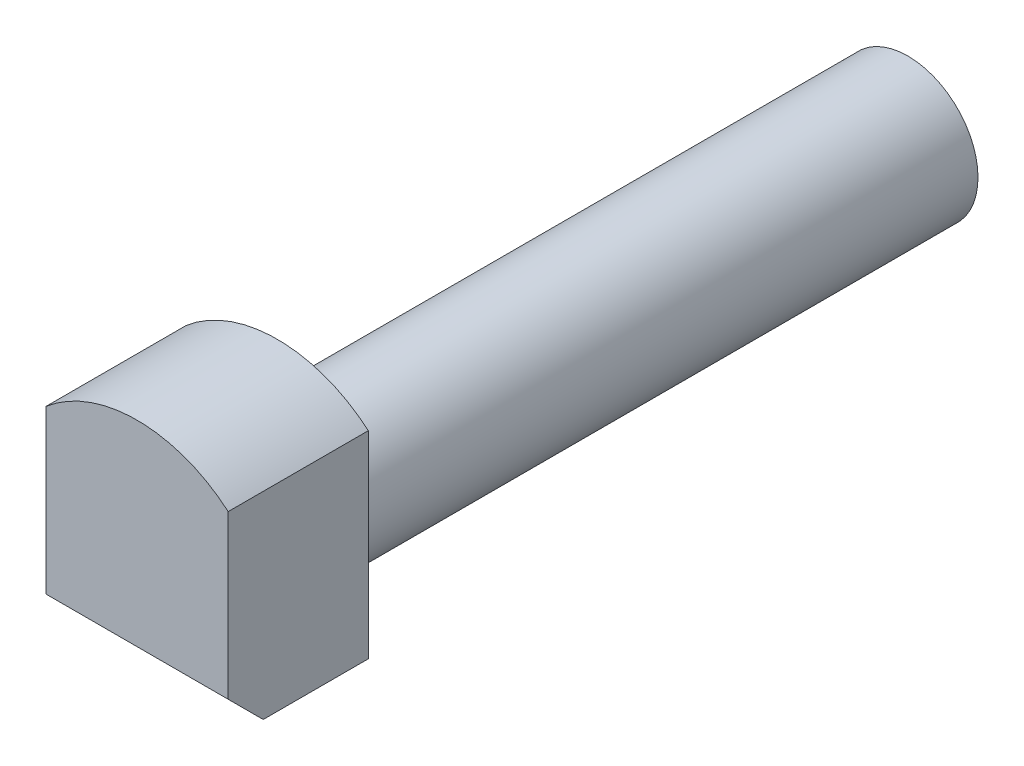
SolidWorks part; units mm, degrees
ref_plane "Plan de face" through (0, 0, 0) normal (0, 0, 1) x (1, 0, 0)
ref_plane "Plan de dessus" through (0, 0, 0) normal (0, 1, 0) x (1, 0, 0)
ref_plane "Plan de droite" through (0, 0, 0) normal (1, 0, 0) x (0, 0, -1)
sketch "Esquisse1" plane through (0, 0, 0) normal (0, 0, 1) x (1, 0, 0)
  circle A2 centre (2.7, 1.35) radius 1 construction
  circle A3 centre (2.7, 1.35) radius 1
extrude "Boss.-Extru.1" add sketch "Esquisse1" along normal blind 3.5 and the other way offset from surface (11 mm away) 1
sketch "Esquisse2" plane through (0, 0, 3.5) normal (0, 0, 1) x (1, 0, 0)
  circle A0 centre (2.7, 1.35) radius 2
  dimension "D1" = 4
extrude "Boss.-Extru.2" add sketch "Esquisse2" along normal blind 2
sketch "Esquisse3" plane through (0, 0, 5.5) normal (0, 0, 1) x (1, 0, 0)
  line L0 (1.4, 2.8699) -> (1.4, 0.05)
  line L1 (1.4, 0.05) -> (4, 0.05)
  line L2 (4, 0.05) -> (4, 2.8699)
  line L3 (2.7, 1.35) -> (2.7, 5.1243) construction
  circle A0 centre (2.7, 1.35) radius 2 construction
  circle A1 centre (2.7, 1.35) radius 1 construction
  arc A2 (4, 2.8699) -> (1.4, 2.8699) centre (2.7, 1.35) ccw
  dimension "D2" = 1.3
  dimension "D1" = 2.6
extrude "Enlèv. mat.-Extru.1" cut sketch "Esquisse3" against normal through all and the other way through all flip side to cut
chamfer "Chanfrein1" distance 0.5 angle 45 1 edges at (2.7, 0.05, 5.5)
sketch "Esquisse4" plane through (0, 0, -11) normal (0, 0, -1) x (-1, 0, 0)
  circle A1 centre (-2.7, 1.35) radius 1
  circle A2 centre (-2.7, 1.35) radius 1
  dimension "D1" = 0
extrude "Enlèv. mat.-Extru.2" cut sketch "Esquisse4" against normal blind 5.5
